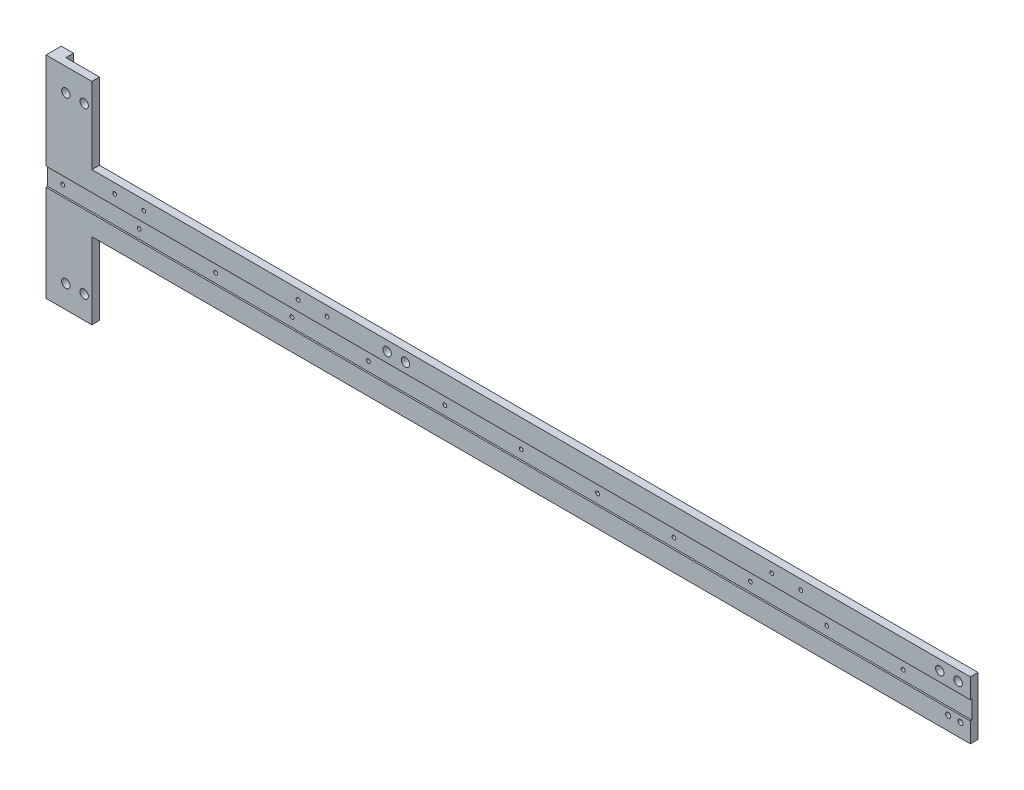
SolidWorks part; units mm, degrees
ref_plane "前视基准面" through (0, 0, 0) normal (0, 0, 1) x (1, 0, 0)
ref_plane "上视基准面" through (0, 0, 0) normal (0, 1, 0) x (1, 0, 0)
ref_plane "右视基准面" through (0, 0, 0) normal (1, 0, 0) x (0, 0, -1)
sketch "草图1" plane through (0, 0, 0) normal (0, 0, 1) x (1, 0, 0)
  line L1 (0, 0) -> (595, 0)
  line L2 (0, 0) -> (0, 38)
  line L3 (0, 38) -> (595, 38)
  line L4 (595, 0) -> (595, 38)
  dimension "D1" = 38
  dimension "D2" = 595
extrude "凸台-拉伸1" add sketch "草图1" along normal blind 5
hole_wizard "M3 螺纹孔1" positions "草图2" profile "草图3" tap size "M3" standard "ISO" end condition through all
sketch "草图2" plane through (0, 0, 5) normal (0, 0, 1) x (1, 0, 0)
  line L0 (0, 19) -> (40.9231, 19) construction
  line L1 (0, 38) -> (0, 0) construction
  point P0 (10, 19)
  dimension "D1" = 10
sketch "草图3" plane through (10, 19, 5) normal (1, 0, 0) x (0, -1, 0)
  line L0 (0, 0) -> (0, 5)
  line L1 (0, 5) -> (1.25, 5)
  line L2 (1.25, 5) -> (1.25, 0)
  line L5 (1.25, 0) -> (0, 0)
  line L11 (0, -6.35) -> (0, 107.95) construction
  dimension "通孔螺纹孔钻头直径" = 2.5
  dimension "通孔螺纹孔钻头深度" = 5
cosmetic thread "孔螺蚊线1" parameters "D2"=3
pattern_linear "阵列(线性)1" count 12 spacing 50 along (1, 0, 0) of "M3 螺纹孔1"
sketch "草图4" plane through (0, 0, 5) normal (0, 0, 1) x (1, 0, 0)
  line L0 (0, 19) -> (90.1433, 19) construction
  line L1 (0, 38) -> (0, 0) construction
  line L2 (595, 0) -> (595, 38) construction
  line L3 (0, 25) -> (595, 25)
  line L4 (0, 25) -> (0, 13)
  line L5 (0, 13) -> (595, 13)
  line L6 (595, 25) -> (595, 13)
  dimension "D1" = 12
extrude "切除-拉伸1" cut sketch "草图4" against normal blind 1
sketch "草图5" plane through (0, 0, 0) normal (-1, 0, 0) x (0, 0, 1)
  line L1 (0, 38) -> (-5, 38)
  line L2 (0, 38) -> (0, 0)
  line L3 (0, 0) -> (-5, 0)
  line L4 (-5, 38) -> (-5, 0)
  dimension "D1" = 5
extrude "凸台-拉伸2" add sketch "草图5" against normal blind 8
hole_wizard "M4 螺纹孔1" positions "草图6" profile "草图7" tap size "M4" standard "ISO"
sketch "草图6" plane through (0, 0, 0) normal (-1, 0, 0) x (0, 0, 1)
  point P0 (0.6955, 14)
  point P3 (0.6955, 4)
sketch "草图7" plane through (0, 14, 0.6955) normal (0, 1, 0) x (0, 0, 1)
  line L0 (0, 0) -> (0, 6.9914)
  line L1 (0, 6.9914) -> (1.65, 6)
  line L2 (1.65, 6) -> (1.65, 0)
  line L5 (1.65, 0) -> (0, 0)
  line L10 (0, 6.9914) -> (-1.65, 6) construction
  line L11 (0, -6.35) -> (0, 107.95) construction
  dimension "螺纹孔钻头直径" = 3.3
  dimension "螺纹孔钻头深度" = 6
  dimension "导头角度" = 118
cosmetic thread "孔螺蚊线2" parameters "D1"=6, "D2"=4
cosmetic thread "孔螺蚊线3" parameters "D1"=6, "D2"=4
sketch "草图8" plane through (595, 0, 0) normal (1, 0, 0) x (0, 0, -1)
  line L0 (-5, 0) -> (-5, 13)
  line L1 (-5, 13) -> (-4, 13)
  line L2 (-4, 13) -> (-4, 25)
  line L3 (-4, 25) -> (-5, 25)
  line L4 (-5, 25) -> (-5, 38)
  line L5 (-5, 38) -> (0, 38)
  line L6 (0, 38) -> (0, 0)
  line L7 (0, 0) -> (-5, 0)
extrude "凸台-拉伸3" add sketch "草图8" along normal blind 10
hole_wizard "M4 螺纹孔2" positions "草图9" profile "草图10" tap size "M4" standard "ISO"
sketch "草图9" plane through (0, 0, 5) normal (0, 0, 1) x (1, 0, 0)
  line L0 (0, 0) -> (605, 0) construction
  line L1 (605, 13) -> (605, 0) construction
  point P3 (598.5, 9.0024)
  point P10 (590.5, 9.0024)
  dimension "D1" = 9.0024
  dimension "D2" = 6.5
  dimension "D3" = 8
sketch "草图10" plane through (598.5, 9.0024, 5) normal (1, 0, 0) x (0, -1, 0)
  line L0 (0, 0) -> (0, 11.0914)
  line L1 (0, 11.0914) -> (1.65, 10.1)
  line L2 (1.65, 10.1) -> (1.65, 0)
  line L5 (1.65, 0) -> (0, 0)
  line L10 (0, 11.0914) -> (-1.65, 10.1) construction
  line L11 (0, -6.35) -> (0, 107.95) construction
  dimension "螺纹孔钻头直径" = 3.3
  dimension "螺纹孔钻头深度" = 10.1
  dimension "导头角度" = 118
cosmetic thread "孔螺蚊线4" parameters "D1"=5, "D2"=4
cosmetic thread "孔螺蚊线5" parameters "D1"=5, "D2"=4
hole_wizard "M3 螺纹孔2" positions "草图12" profile "草图13" tap size "M3" standard "ISO"
sketch "草图12" plane through (0, 0, 0) normal (0, 0, -1) x (-1, 0, 0)
  point P0 (-44.9928, 31.7)
  point P3 (-63.9928, 31.7)
sketch "草图13" plane through (44.9928, 31.7, 0) normal (1, 0, 0) x (0, 1, 0)
  line L0 (0, 0) -> (0, 8.2511)
  line L1 (0, 8.2511) -> (1.25, 7.5)
  line L2 (1.25, 7.5) -> (1.25, 0)
  line L5 (1.25, 0) -> (0, 0)
  line L10 (0, 8.2511) -> (-1.25, 7.5) construction
  line L11 (0, -6.35) -> (0, 107.95) construction
  dimension "螺纹孔钻头直径" = 2.5
  dimension "螺纹孔钻头深度" = 7.5
  dimension "导头角度" = 118
cosmetic thread "孔螺蚊线6" parameters "D1"=5, "D2"=3
cosmetic thread "孔螺蚊线7" parameters "D1"=5, "D2"=3
pattern_linear "阵列(线性)2" count 2 spacing 120 along (1, 0, 0) of "M3 螺纹孔2"
pattern_linear "阵列(线性)3" count 2 spacing 430 along (1, 0, 0) of "M3 螺纹孔2"
sketch "草图14" plane through (0, 0, 0) normal (0, -1, 0) x (1, 0, 0)
  line L0 (8, -5) -> (0, -5)
  line L1 (0, -5) -> (0, 5)
  line L2 (0, 5) -> (30, 5)
  line L3 (0, 5) -> (605, 5) construction
  line L4 (30, 5) -> (30, 0)
  line L5 (8, 0) -> (605, 0) construction
  line L6 (30, 0) -> (8, 0)
  line L7 (8, 0) -> (8, -5)
  dimension "D1" = 30
extrude "凸台-拉伸4" add sketch "草图14" along normal blind 50
sketch "草图15" plane through (0, 38, 0) normal (0, 1, 0) x (1, 0, 0)
  line L0 (0, 5) -> (0, -5)
  line L1 (0, -5) -> (30, -5)
  line L2 (605, -5) -> (0, -5) construction
  line L3 (30, -5) -> (30, 0)
  line L4 (605, 0) -> (8, 0) construction
  line L5 (30, 0) -> (8, 0)
  line L6 (8, 0) -> (8, 5)
  line L7 (8, 5) -> (0, 5)
  dimension "D1" = 30
extrude "凸台-拉伸5" add sketch "草图15" along normal blind 50
sketch "草图18" plane through (0, 0, 5) normal (0, 0, 1) x (1, 0, 0)
  line L0 (25, 73) -> (13, 73) construction
  line L1 (13, 73) -> (19, 73) construction
  line L2 (19, 73) -> (19, 54.0756) construction
  line L3 (30, 88) -> (30, 38) construction
  line L4 (0, 88) -> (30, 88) construction
  line L5 (0, 25) -> (0, 13) construction
  line L6 (0, 13) -> (0, 19) construction
  line L7 (0, 19) -> (32.4906, 19) construction
  circle A0 centre (25, 73) radius 2.75
  circle A1 centre (13, 73) radius 2.75
  circle A2 centre (13, -35) radius 2.75
  circle A3 centre (25, -35) radius 2.75
  dimension "D1" = 5.5
  dimension "D2" = 5.5
  dimension "D3" = 12
  dimension "D4" = 11
  dimension "D5" = 15
extrude "切除-拉伸2" cut sketch "草图18" against normal blind 8
sketch "草图19" plane through (0, 0, 5) normal (0, 0, 1) x (1, 0, 0)
  line L0 (605, 31.5) -> (569.1108, 31.5) construction
  line L1 (605, 38) -> (605, 25) construction
  circle A0 centre (585, 31.5) radius 2.75
  circle A1 centre (597, 31.5) radius 2.75
  dimension "D1" = 5.5
  dimension "D2" = 5.5
  dimension "D3" = 12
  dimension "D4" = 8
extrude "切除-拉伸3" cut sketch "草图19" against normal blind 8
sketch "草图20" plane through (0, 0, 5) normal (0, 0, 1) x (1, 0, 0)
  line L0 (204.3443, 25) -> (204.3443, 38) construction
  line L1 (605, 25) -> (0, 25) construction
  line L2 (605, 38) -> (30, 38) construction
  line L3 (204.3443, 38) -> (204.3443, 31.5) construction
  line L4 (204.3443, 31.5) -> (254.0304, 31.5) construction
  circle A0 centre (235.2886, 31.5) radius 2.75
  circle A1 centre (223.2886, 31.5) radius 2.75
  dimension "D1" = 5.5
  dimension "D2" = 5.5
  dimension "D3" = 12
extrude "切除-拉伸4" cut sketch "草图20" against normal blind 8
